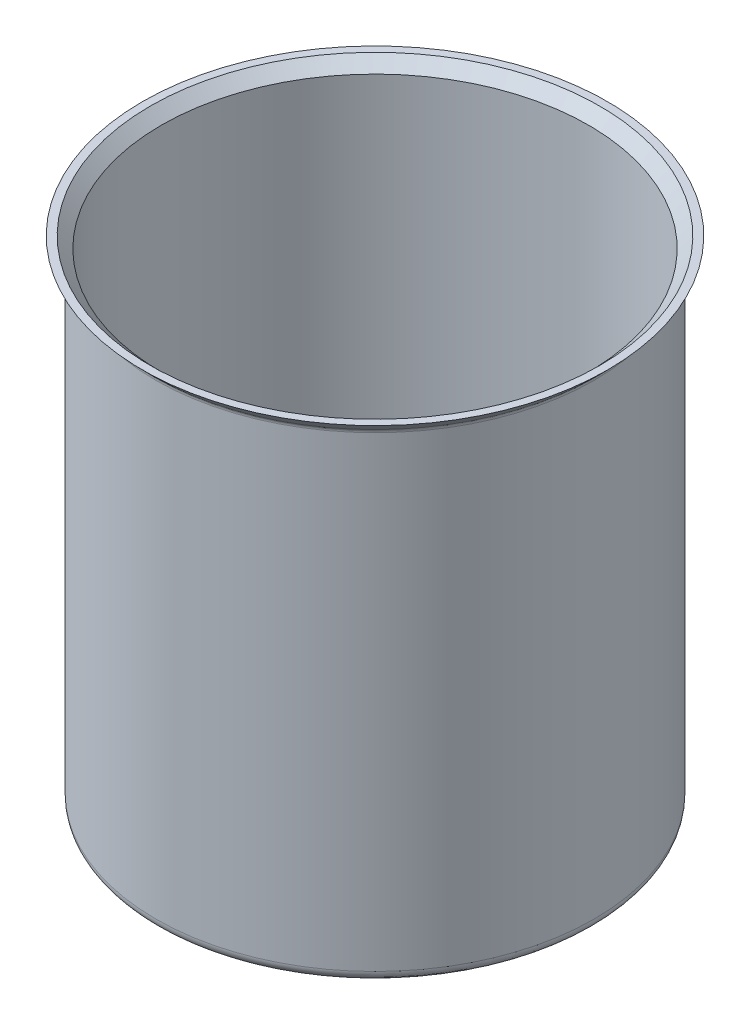
SolidWorks part; units mm, degrees
ref_plane "Plano frontal" through (0, 0, 0) normal (0, 0, 1) x (1, 0, 0)
ref_plane "Plano superior" through (0, 0, 0) normal (0, 1, 0) x (1, 0, 0)
ref_plane "Plano direito" through (0, 0, 0) normal (1, 0, 0) x (0, 0, -1)
sketch "Sketch1" plane through (0, 0, 0) normal (0, 0, 1) x (1, 0, 0)
  line L0 (0, 51.358) -> (0, -38.642) construction
  line L1 (0, -38.642) -> (40, -38.642)
  line L2 (40, -38.642) -> (40, 48.9268)
  line L3 (40, 48.9268) -> (42.4311, 51.358)
  line L4 (42.4311, 51.358) -> (0, 51.358)
  line L5 (0, 51.358) -> (0, -38.642)
  dimension "D1" = 40
  dimension "D2" = 90
revolve "Revolve1" add sketch "Sketch1" angle 360 about L5
shell "Shell2" thickness 1
fillet "Fillet1" radius 2 1 edges at (-40, -38.642, 0)
fillet "Fillet2" radius 1 1 edges at (-40, 48.9268, 0)
